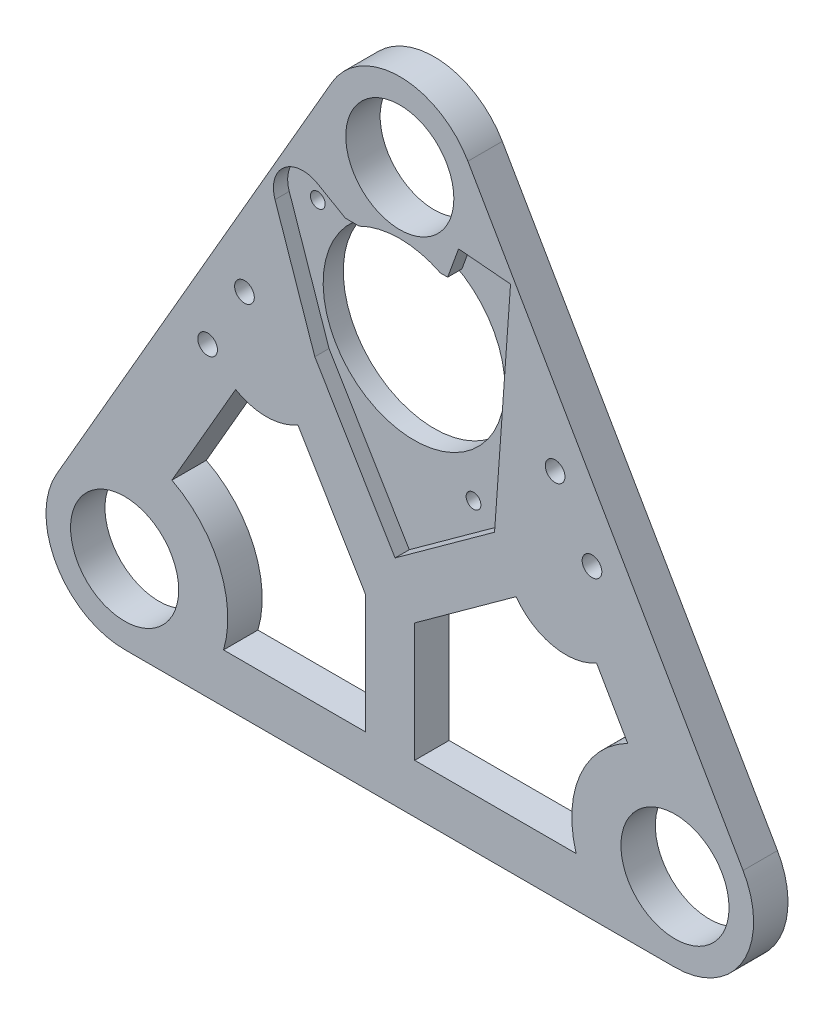
SolidWorks part; units mm, degrees
ref_plane "Front Plane" through (0, 0, 0) normal (0, 0, 1) x (1, 0, 0)
ref_plane "Top Plane" through (0, 0, 0) normal (0, 1, 0) x (1, 0, 0)
ref_plane "Right Plane" through (0, 0, 0) normal (1, 0, 0) x (0, 0, -1)
sketch "Sketch1" plane through (0, 0, 0) normal (0, 0, 1) x (1, 0, 0)
  line L0 (3.85, 0) -> (-3.85, 0) construction
  line L1 (42.1436, 104.9948) -> (-13.8564, 8)
  line L2 (69.8564, 104.9948) -> (125.8564, 8)
  line L3 (0, -16) -> (112, -16)
  circle A0 centre (0, 0) radius 11
  circle A1 centre (112, 0) radius 11
  arc A2 (-13.8564, 8) -> (0, -16) centre (0, 0) ccw
  arc A3 (112, -16) -> (125.8564, 8) centre (112, 0) ccw
  circle A4 centre (56, 96.9948) radius 11
  arc A5 (69.8564, 104.9948) -> (42.1436, 104.9948) centre (56, 96.9948) ccw
  dimension "D1" = 22
  dimension "D2" = 22
  dimension "D3" = 32
  dimension "D4" = 32
  dimension "D5" = 112
  dimension "D6" = 22
  dimension "D7" = 32
  dimension "D8" = 112
  dimension "D9" = 112
extrude "Boss-Extrude1" add sketch "Sketch1" along normal blind 7
sketch "Sketch3" plane through (0, 0, 7) normal (0, 0, 1) x (1, 0, 0)
  line L0 (56, 71.0948) -> (56, 69.0948) construction
  circle A0 centre (56, 96.9948) radius 27.9 construction
  circle A1 centre (56, 65.9448) radius 5.15 construction
  circle A2 centre (56, 65.9448) radius 18.5
  dimension "D1" = 55.8
  dimension "D2" = 10.3
  dimension "D4" = 37
  dimension "D3" = 2
extrude "Cut-Extrude1" cut sketch "Sketch3" against normal through all
sketch "Sketch4" plane through (0, 0, 7) normal (0, 0, 1) x (1, 0, 0)
  line L0 (44.91, 82.4948) -> (65.74, 82.4948)
  line L1 (65.74, 82.4948) -> (67.9631, 88.6028)
  line L2 (67.9631, 88.6028) -> (78.5352, 87.6779)
  line L3 (78.5352, 87.6779) -> (75.2824, 42.3244)
  line L4 (75.2824, 42.3244) -> (55.0308, 27.6659)
  line L5 (55.0308, 27.6659) -> (38.7013, 54.953)
  line L6 (38.7013, 54.953) -> (30.6042, 78.6054)
  line L7 (44.91, 82.4948) -> (39.2808, 85.7448)
  line L8 (56, 65.9448) -> (56, 82.4948) construction
  line L9 (56, 65.9448) -> (63.15, 65.9448) construction
  circle A0 centre (56, 65.9448) radius 7.15 construction
  arc A1 (39.2808, 85.7448) -> (30.6042, 78.6054) centre (36.2808, 80.5487) ccw
  dimension "D1" = 14.3
  dimension "D8" = 12
  dimension "D15" = 16.55
  dimension "D2" = 85
  dimension "D3" = 130
  dimension "D4" = 168
  dimension "D5" = 105
  dimension "D6" = 250
  dimension "D7" = 210
  dimension "D9" = 25
  dimension "D10" = 31.8
  dimension "D11" = 25
  dimension "D12" = 45.47
  dimension "D13" = 6.5
  dimension "D14" = 20.83
  dimension "D16" = 90
  dimension "D17" = 11.09
  dimension "D18" = 6.5
extrude "Cut-Extrude2" cut sketch "Sketch4" against normal blind 2.9
sketch "Sketch5" plane through (0, 0, 7) normal (0, 0, 1) x (1, 0, 0)
  line L0 (22.5915, 41.1297) -> (9.6221, 18.6659)
  line L1 (42.1436, 104.9948) -> (-13.8564, 8) construction
  line L2 (20.1246, -6) -> (49.0315, -6)
  line L3 (35.2604, 41.2289) -> (49.0315, 18.217)
  line L4 (49.0315, 18.217) -> (49.0315, -6)
  line L5 (59.0315, 18.217) -> (59.0315, -6)
  line L6 (38.7013, 54.953) -> (55.0308, 27.6659) construction
  line L7 (38.7013, 54.953) -> (55.0308, 27.6659) construction
  line L8 (0, -16) -> (112, -16) construction
  line L9 (96.0352, 29.6518) -> (102.3779, 18.6659)
  line L10 (125.8564, 8) -> (69.8564, 104.9948) construction
  line L11 (79.6594, 33.1479) -> (59.0315, 18.217)
  line L12 (55.0308, 27.6659) -> (75.2824, 42.3244) construction
  line L13 (59.0315, -6) -> (91.8754, -6)
  line L14 (28.8415, 51.955) -> (22.5915, 41.1297) construction
  line L15 (28.8415, 51.955) -> (35.2604, 41.2289) construction
  line L16 (89.7852, 40.4771) -> (79.6594, 33.1479) construction
  line L17 (89.7852, 40.4771) -> (96.0352, 29.6518) construction
  arc A0 (20.1246, -6) -> (9.6221, 18.6659) centre (0, 0) ccw
  circle A1 centre (0, 0) radius 11 construction
  arc A2 (102.3779, 18.6659) -> (91.8754, -6) centre (112, 0) ccw
  circle A3 centre (112, 0) radius 11 construction
  arc A4 (22.5915, 41.1297) -> (35.2604, 41.2289) centre (28.8415, 51.955) ccw
  arc A5 (79.6594, 33.1479) -> (96.0352, 29.6518) centre (89.7852, 40.4771) ccw
  dimension "D1" = 10
  dimension "D5" = 10
  dimension "D9" = 25
  dimension "D10" = 25
  dimension "D2" = 15
  dimension "D3" = 10
  dimension "D4" = 10
  dimension "D6" = 10
  dimension "D7" = 15
  dimension "D8" = 10
extrude "Cut-Extrude3" cut sketch "Sketch5" against normal through all
sketch "Sketch7" plane through (0, 0, 4.1) normal (0, 0, 1) x (1, 0, 0)
  line L0 (75.2824, 42.3244) -> (68.1009, 42.8395) construction
  line L1 (78.5352, 87.6779) -> (75.2824, 42.3244) construction
  circle A0 centre (68.1009, 42.8395) radius 1.5
  circle A1 centre (36.41, 79.9948) radius 1.5
  dimension "D2" = 3
  dimension "D5" = 3
  dimension "D1" = 7.2
  dimension "D3" = 8.5
  dimension "D4" = 2.5
  dimension "D6" = 90
extrude "Cut-Extrude4" cut sketch "Sketch7" against normal through all
sketch "Sketch10" plane through (0, 0, 7) normal (0, 0, 1) x (1, 0, 0)
  line L0 (24.3888, 59.2426) -> (16.8888, 46.2522) construction
  line L1 (42.1436, 104.9948) -> (-13.8564, 8) construction
  line L2 (20.6388, 52.7474) -> (14.1436, 56.4974) construction
  line L3 (87.6112, 59.2426) -> (95.1112, 46.2522) construction
  line L4 (125.8564, 8) -> (69.8564, 104.9948) construction
  circle A0 centre (24.3888, 59.2426) radius 2
  circle A1 centre (16.8888, 46.2522) radius 2
  circle A2 centre (87.6112, 59.2426) radius 2
  circle A3 centre (95.1112, 46.2522) radius 2
  dimension "D1" = 4
  dimension "D2" = 4
  dimension "D4" = 4
  dimension "D5" = 4
  dimension "D3" = 15
  dimension "D6" = 7.5
  dimension "D7" = 7.5
extrude "Cut-Extrude5" cut sketch "Sketch10" against normal through all
